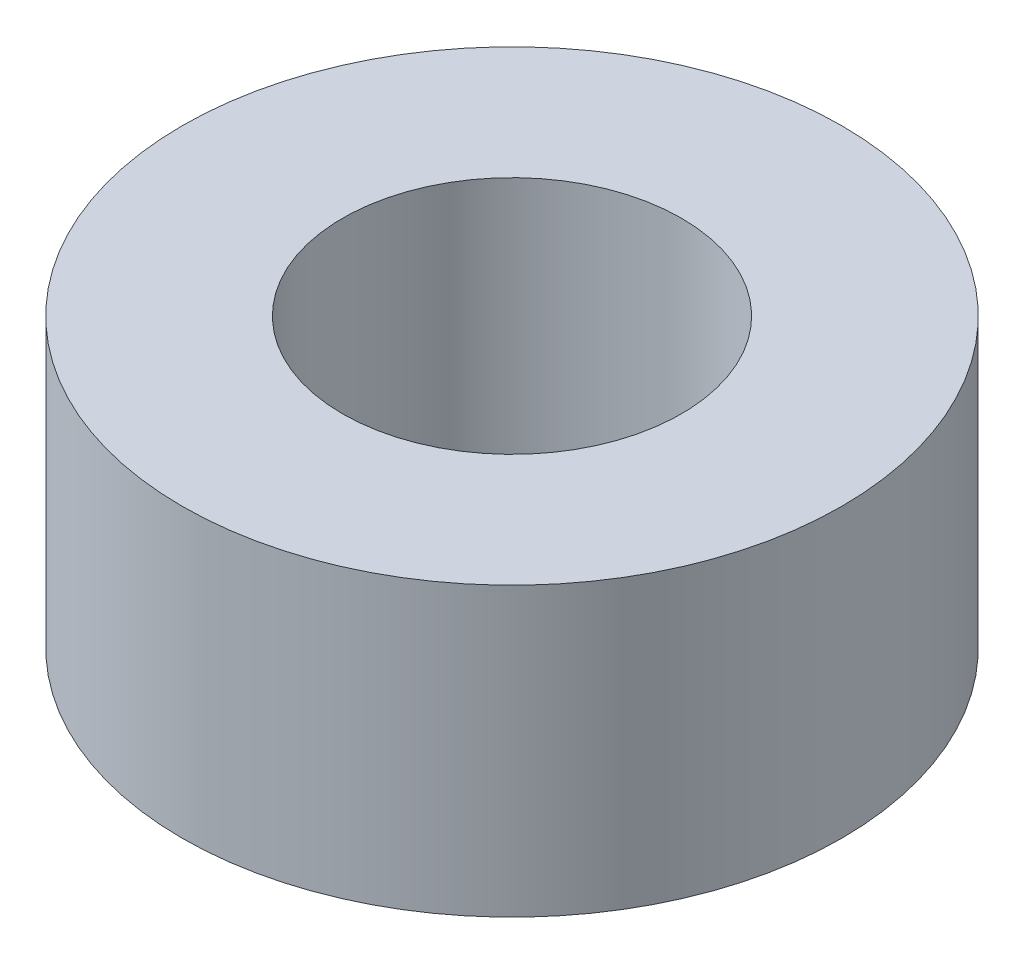
SolidWorks part; units mm, degrees
material "Nylon 101"
ref_plane "Front Plane" through (0, 0, 0) normal (0, 0, 1) x (1, 0, 0)
ref_plane "Top Plane" through (0, 0, 0) normal (0, 1, 0) x (1, 0, 0)
ref_plane "Right Plane" through (0, 0, 0) normal (1, 0, 0) x (0, 0, -1)
sketch "Sketch1" plane through (0, 0, 0) normal (0, 1, 0) x (1, 0, 0)
  circle A0 centre (0, 0) radius 3.2639
  circle A1 centre (0, 0) radius 6.35
  dimension "D1" = 6.5278
  dimension "D2" = 12.7
extrude "Boss-Extrude1" add sketch "Sketch1" along normal blind 5.5372
